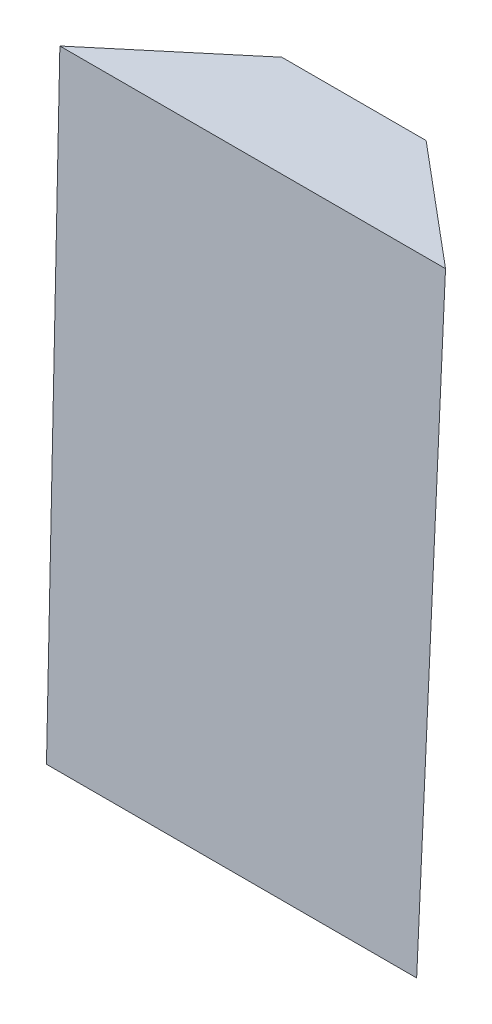
SolidWorks part; units mm, degrees
ref_plane "Alzado" through (0, 0, 0) normal (0, 0, 1) x (1, 0, 0)
ref_plane "Planta" through (0, 0, 0) normal (0, 1, 0) x (1, 0, 0)
ref_plane "Vista lateral" through (0, 0, 0) normal (1, 0, 0) x (0, 0, -1)
sketch "Croquis1" plane through (0, 0, 0) normal (0, 1, 0) x (1, 0, 0)
  line L0 (0, 0) -> (45.7, 0)
  line L1 (45.7, 0) -> (30.7986, 12.5)
  line L2 (30.7986, 12.5) -> (14.8886, 12.5)
  line L3 (14.8886, 12.5) -> (0, 0)
  point P3 (10.4406, 12.5)
  dimension "D1" = 12.5
  dimension "D2" = 45.7
  dimension "D3" = 19.45
  dimension "D4" = 15.91
ref_plane "Plano1" through (0, 75, 0) normal (0, 1, 0) x (1, 0, 0)
sketch "Croquis2" plane through (0, 75, 0) normal (0, 1, 0) x (1, 0, 0)
  line L0 (13.9286, 15.12) -> (31.7486, 15.12)
  line L1 (31.7486, 15.12) -> (46.6436, 2.62)
  line L2 (46.6436, 2.62) -> (-0.9664, 2.62)
  line L3 (-0.9664, 2.62) -> (13.9286, 15.12)
  line L4 (22.8386, 2.62) -> (22.8386, 35.3921) construction
  line L5 (30.7986, 12.5) -> (30.7986, 15.12) construction
  line L6 (30.7986, 15.12) -> (31.7486, 15.12) construction
  point P9 (0, 0)
  dimension "D1" = 17.82
  dimension "D2" = 47.61
  dimension "D3" = 12.5
  dimension "D4" = 0.95
  dimension "D5" = 2.62
loft "Recubrir1" add profiles "Croquis2", "Croquis1"
